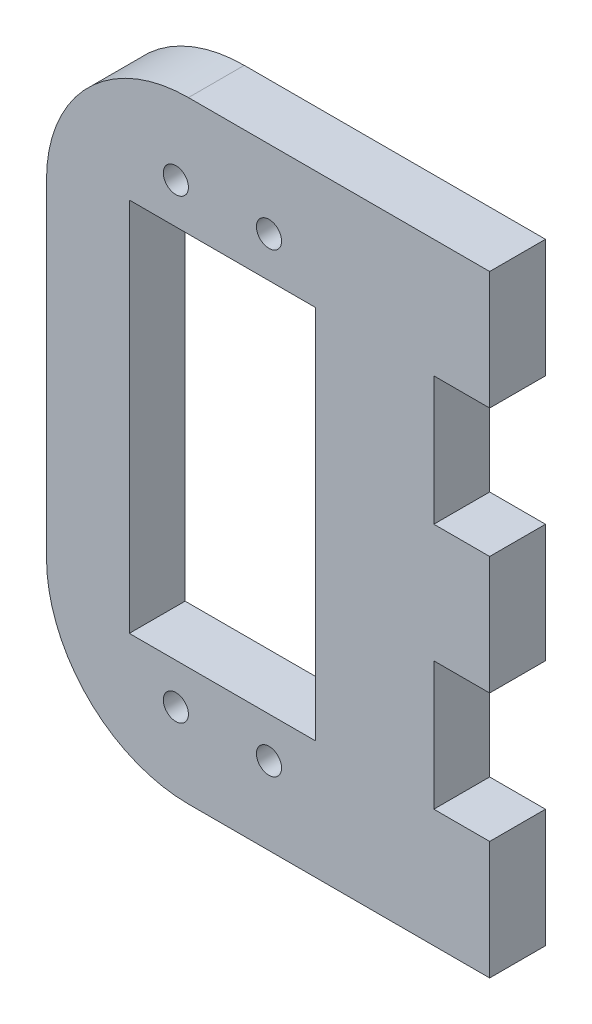
SolidWorks part; units mm, degrees
ref_plane "Front Plane" through (0, 0, 0) normal (0, 0, 1) x (1, 0, 0)
ref_plane "Top Plane" through (0, 0, 0) normal (0, 1, 0) x (1, 0, 0)
ref_plane "Right Plane" through (0, 0, 0) normal (1, 0, 0) x (0, 0, -1)
sketch "Sketch1" plane through (0, 0, 0) normal (0, 0, 1) x (1, 0, 0)
  line L0 (-10, 20.15) -> (10, 20.15)
  line L1 (10, 20.15) -> (10, -20.15)
  line L2 (10, -20.15) -> (-10, -20.15)
  line L3 (-10, 20.15) -> (-10, -20.15)
  line L4 (-18.89, -17.61) -> (-18.89, 17.61)
  line L6 (22.7, 32.85) -> (28.6944, 32.85)
  line L7 (28.6944, 32.85) -> (28.6944, 20.15)
  line L8 (-3.65, -32.85) -> (22.7, -32.85)
  line L9 (28.6944, 20.15) -> (22.7, 20.15)
  line L10 (10, 32.85) -> (-3.65, 32.85)
  line L11 (22.7, -32.85) -> (28.6944, -32.85)
  line L12 (28.6944, -32.85) -> (28.6944, -20.15)
  line L13 (10, 32.85) -> (22.7, 32.85)
  line L14 (22.7, 20.15) -> (22.7, 6.35)
  line L15 (28.6944, -20.15) -> (22.7, -20.15)
  line L17 (28.6944, 0) -> (28.6944, 6.35)
  line L18 (28.6944, 6.35) -> (22.7, 6.35)
  line L19 (28.6944, 0) -> (28.6944, -6.35)
  line L20 (28.6944, -6.35) -> (22.7, -6.35)
  line L21 (22.7, -6.35) -> (22.7, -20.15)
  circle A0 centre (-5, -24.5) radius 1.35
  circle A1 centre (5, -24.5) radius 1.35
  circle A2 centre (-5, 24.5) radius 1.35
  circle A3 centre (5, 24.5) radius 1.35
  arc A4 (-18.89, -17.61) -> (-3.65, -32.85) centre (-3.65, -17.61) ccw
  arc A5 (-18.89, 17.61) -> (-3.65, 32.85) centre (-3.65, 17.61) cw
  dimension "D1" = 15.24
  dimension "D2" = 15.24
extrude "Boss-Extrude1" add sketch "Sketch1" along normal blind 5.9944 contours A5 L4 A4 L8 L11 L12 L15 L21 L20 L19 L17 L18 L14 L9 L7 L6 L13 L10 A3 A2 A1 A0 L3 L0 L1 L2
